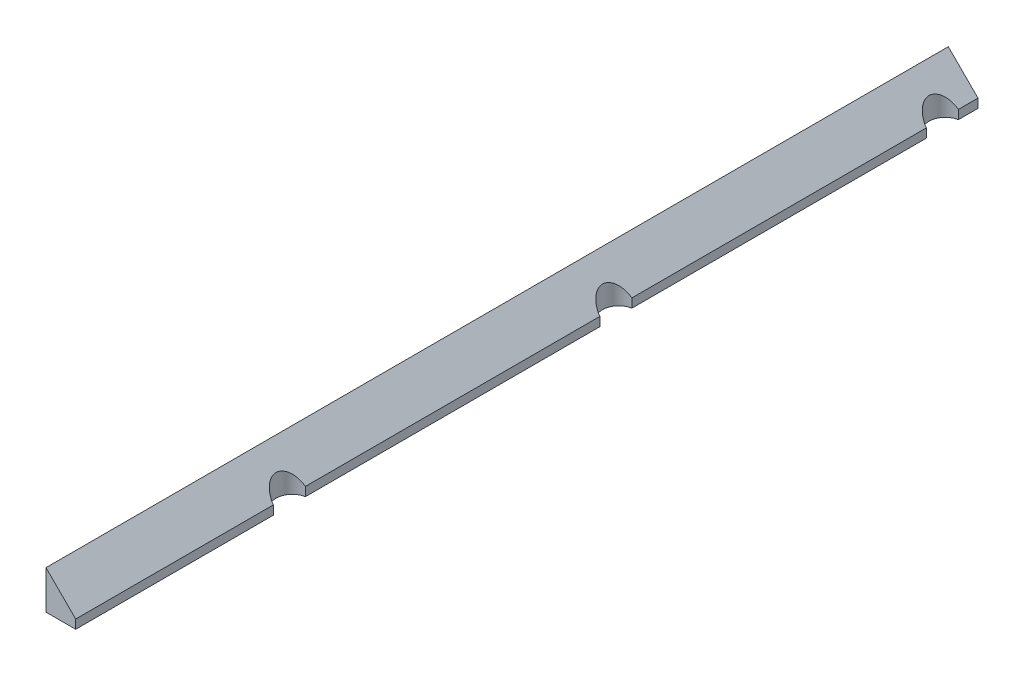
SolidWorks part; units mm, degrees
material "6061-T6 (SS)"
ref_plane "Front Plane" through (0, 0, 0) normal (0, 0, 1) x (1, 0, 0)
ref_plane "Top Plane" through (0, 0, 0) normal (0, 1, 0) x (1, 0, 0)
ref_plane "Right Plane" through (0, 0, 0) normal (1, 0, 0) x (0, 0, -1)
sketch "Sketch1" plane through (0, 0, 0) normal (0, 0, 1) x (1, 0, 0)
  line L5 (0, 0) -> (2.6, 0)
  line L6 (2.6, 0) -> (0, 2.6)
  line L7 (0, 2.6) -> (0, 0)
  line L11 (2, 0) -> (2, 0.6)
  dimension "D1" = 0.6
  dimension "D2" = 2.6
extrude "Boss-Extrude1" add sketch "Sketch1" against normal mid plane 72.8 contours L5 L11 L6 L7
sketch "Sketch2" plane through (0, 0, 0) normal (0, -1, 0) x (1, 0, 0)
  line L0 (2, -36.4) -> (2, 36.4) construction
  circle A12 centre (2.2, 0) radius 1.1
  circle A13 centre (2.2, 22) radius 1.1
  circle A14 centre (2.2, -22) radius 1.1
  dimension "D1" = 2.2
  dimension "D2" = 0.2
  dimension "D3" = 22
  dimension "D4" = 22
extrude "Cut-Extrude1" cut sketch "Sketch2" against normal up to surface (0.4 mm away)
sketch "Sketch3" plane through (0, 0, 0) normal (0, -1, 0) x (1, 0, 0)
  line L1 (2, -20.9183) -> (2, -1.0817) construction
  circle A0 centre (2.2, 0) radius 1
  dimension "D1" = 2
  dimension "D2" = 0.2
extrude "Cut-Extrude2" [suppressed] cut sketch "Sketch3" against normal up to surface (0.4 mm away)
sketch "Sketch4" plane through (0, 0, 0) normal (0, -1, 0) x (-1, 0, 0)
  line L0 (0, 36.4) -> (0, -36.4) construction
  line L1 (-2, 36.4) -> (0, 36.4)
  line L2 (-2, 36.4) -> (-2, 24.4)
  line L3 (-2, 24.4) -> (0, 24.4)
  line L4 (0, 36.4) -> (0, 24.4)
  dimension "D1" = 12
extrude "Cut-Extrude3" cut sketch "Sketch4" against normal up to vertex
